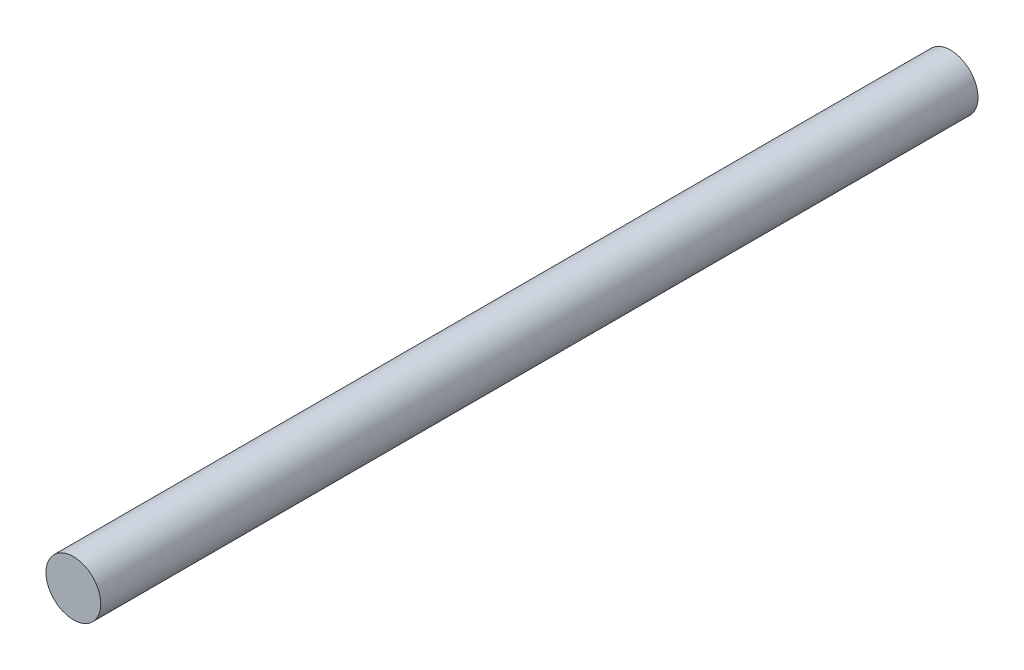
SolidWorks part; units mm, degrees
material "Nylon 101"
ref_plane "Front Plane" through (0, 0, 0) normal (0, 0, 1) x (1, 0, 0)
ref_plane "Top Plane" through (0, 0, 0) normal (0, 1, 0) x (1, 0, 0)
ref_plane "Right Plane" through (0, 0, 0) normal (1, 0, 0) x (0, 0, -1)
sketch "Sketch2" plane through (0, 0, 0) normal (0, 0, 1) x (1, 0, 0)
  circle A0 centre (0, 0) radius 5
  dimension "D1" = 10
extrude "Boss-Extrude1" add sketch "Sketch2" against normal blind 160
